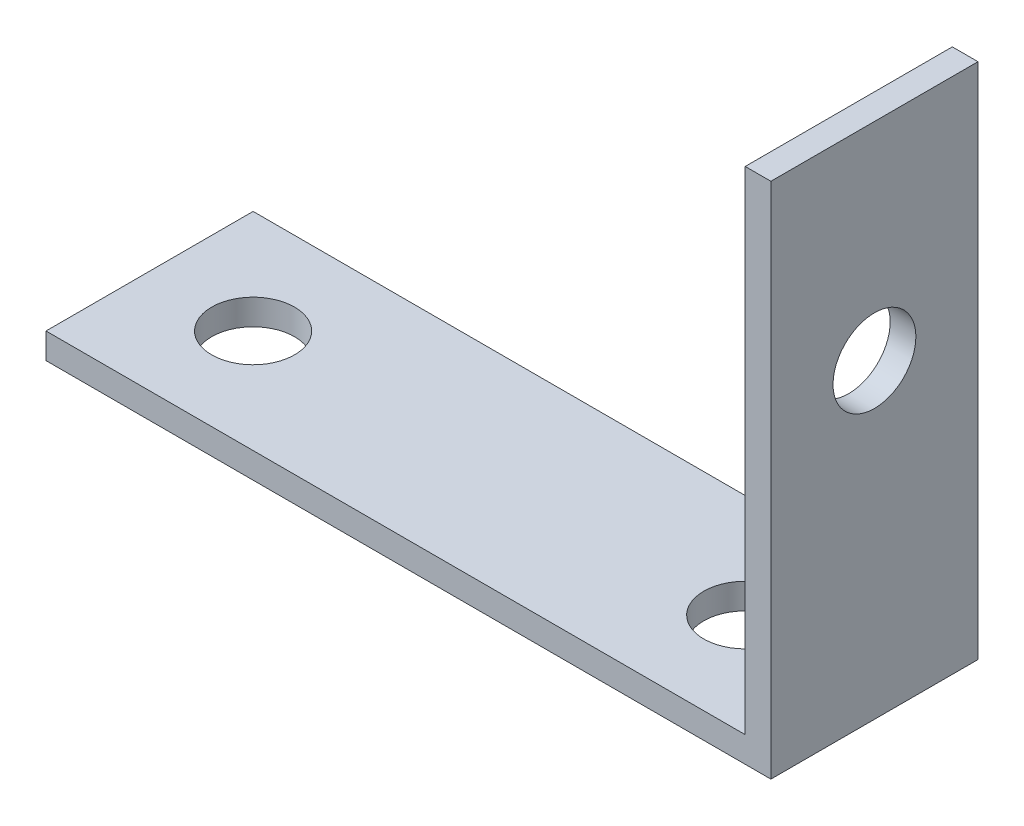
SolidWorks part; units mm, degrees
material "6061 Alloy"
ref_plane "Front Plane" through (0, 0, 0) normal (0, 0, 1) x (1, 0, 0)
ref_plane "Top Plane" through (0, 0, 0) normal (0, 1, 0) x (1, 0, 0)
ref_plane "Right Plane" through (0, 0, 0) normal (1, 0, 0) x (0, 0, -1)
sketch "Sketch1" plane through (0, 0, 0) normal (0, 0, 1) x (1, 0, 0)
  line L0 (0, 0) -> (44.45, 0)
  line L1 (44.45, 0) -> (44.45, 31.75)
  line L2 (44.45, 31.75) -> (42.8752, 31.75)
  line L3 (42.8752, 31.75) -> (42.8752, 1.5748)
  line L4 (42.8752, 1.5748) -> (0, 1.5748)
  line L5 (0, 1.5748) -> (0, 0)
  dimension "D1" = 1.5748
  dimension "D2" = 44.45
  dimension "D3" = 31.75
extrude "Boss-Extrude1" add sketch "Sketch1" along normal blind 12.7
sketch "Sketch2" plane through (42.8752, 0, 0) normal (-1, 0, 0) x (0, 0, 1)
  line L0 (6.35, 31.75) -> (6.35, 1.5748) construction
  line L1 (12.7, 31.75) -> (0, 31.75) construction
  line L2 (12.7, 1.5748) -> (0, 1.5748) construction
  circle A0 centre (6.35, 19.05) radius 2.54
  dimension "D1" = 5.08
  dimension "D2" = 12.7
extrude "Cut-Extrude1" cut sketch "Sketch2" against normal through all
sketch "Sketch3" plane through (0, 1.5748, 0) normal (0, 1, 0) x (1, 0, 0)
  line L0 (0, -6.35) -> (6.35, -6.35) construction
  line L1 (0, -12.7) -> (0, 0) construction
  line L2 (6.35, -6.35) -> (36.5252, -6.35) construction
  line L3 (36.5252, -6.35) -> (42.8752, -6.35) construction
  line L4 (42.8752, -12.7) -> (42.8752, 0) construction
  circle A0 centre (6.35, -6.35) radius 2.54
  circle A1 centre (36.5252, -6.35) radius 2.54
  dimension "D1" = 5.08
  dimension "D2" = 6.35
extrude "Cut-Extrude2" cut sketch "Sketch3" against normal through all
equation "\"base length\" = 21"
equation "\"glass pane length\" = 14.125"
equation "\"glass pane width\" = 10.1875"
equation "\"glass pane wall width\" = 3/4"
equation "\"glass lip\" = 1/4"
equation "\"bolt diameter\" = 0.2"
equation "\"stepper body width\" = 2.22"
equation "\"stepper mount offset\" = 0.19"
equation "\"stepper mount diameter\" = 0.19"
equation "\"stepper shaft offset from body\" = 0.79"
equation "\"stepper spacer thickness\" = 0.2"
equation "\"y axis stepper wall height off base\" = 8"
equation "\"y axis stepper wall bracket thickness\" = 1"
equation "\"y axis stepper wall mount side offset\" = 1/2"
equation "\"y axis stepper wall mount top offset\" = 1/2"
equation "\"y axis stepper wall width\" = \"stepper body width\" + 1                  "
equation "\"y axis bracket height to hole\"= 3.5"
equation "\"thin metal\" = 0.12"
equation "\"thick metal\" = 0.25"
equation "\"foot diameter\"= 0.2"
equation "\"foot inset from corner\"= 1"
equation "\"recognizer width\" = 2.4"
equation "\"recognizer nut plate height\" = 1.25"
equation "\"recognizer nut plate offset\" = 1.5"
equation "\"D1@Sketch2\"=\"bolt diameter\""
equation "\"D1@Sketch3\"=\"bolt diameter\""
equation "\"D3@Sketch1\"=\"recognizer nut plate height\""
